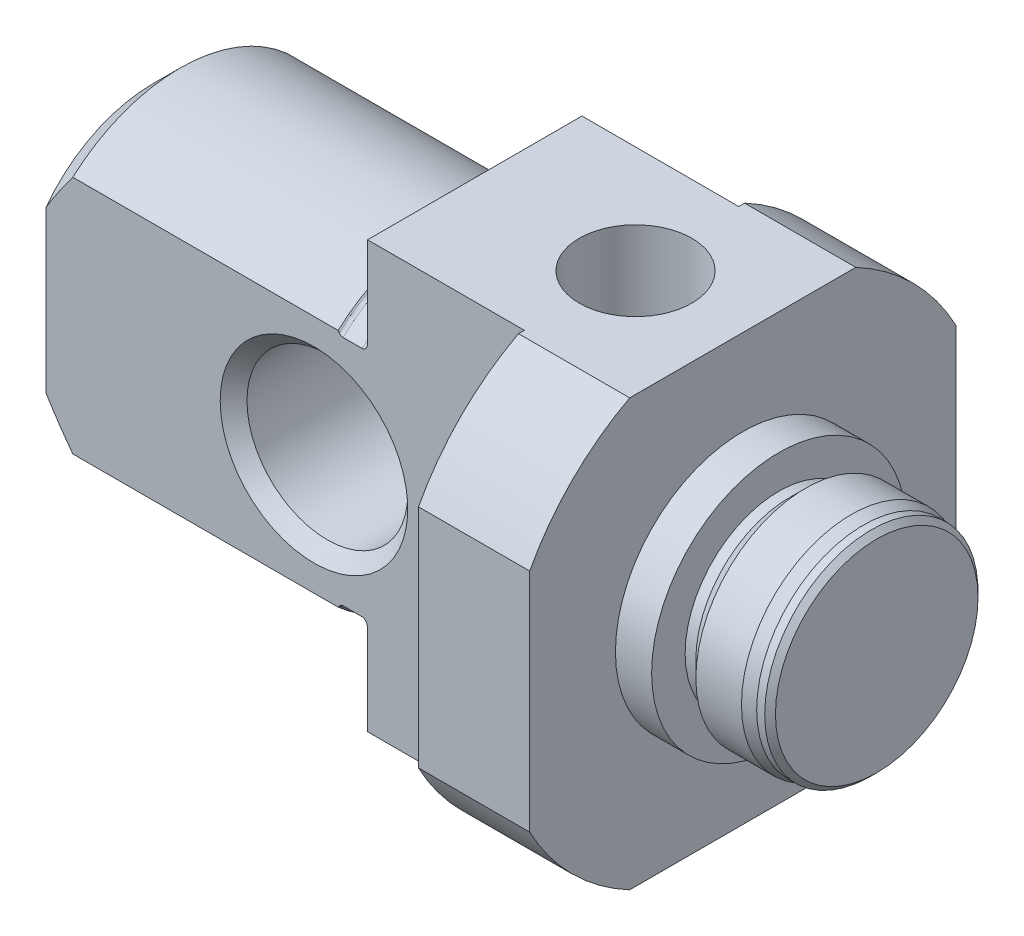
SolidWorks part; units mm, degrees
ref_plane "Front Plane" through (0, 0, 0) normal (0, 0, 1) x (1, 0, 0)
ref_plane "Top Plane" through (0, 0, 0) normal (0, 1, 0) x (1, 0, 0)
ref_plane "Right Plane" through (0, 0, 0) normal (1, 0, 0) x (0, 0, -1)
sketch "Sketch1" plane through (0, 0, 0) normal (0, 0, 1) x (1, 0, 0)
  line L0 (0, 0) -> (10860.2911, 0) construction
  line L1 (0, 0) -> (0, 10860.2911) construction
  line L2 (-22, 0) -> (-22, 5)
  line L3 (-21, 6) -> (-11.1, 6)
  line L4 (-11.1, 6) -> (-11.0586, 5.9586)
  line L5 (-10.9172, 5.9) -> (-10.2, 5.9)
  line L6 (-10, 6.1) -> (-10, 9)
  line L7 (-10, 9) -> (0, 9)
  line L8 (0, 9) -> (0, 4.75)
  line L9 (0, 4.75) -> (1.35, 4.75)
  line L10 (1.35, 4.75) -> (1.35, 3.5)
  line L11 (1.35, 3.5) -> (1.75, 3.5)
  line L12 (1.75, 3.5) -> (2.35, 4.1)
  line L13 (2.35, 4.1) -> (4.0522, 4.1)
  line L14 (4.0522, 4.1) -> (4.5, 3.98)
  line L15 (4.5, 3.98) -> (4.8, 3.98)
  line L16 (5, 3.78) -> (5, 0)
  line L17 (5, 0) -> (-22, 0)
  line L18 (4.8, 3.98) -> (5, 3.78)
  line L19 (-22, 5) -> (-21, 6)
  arc A0 (-10.2, 5.9) -> (-10, 6.1) centre (-10.2, 6.1) ccw
  arc A1 (-11.0586, 5.9586) -> (-10.9172, 5.9) centre (-10.9172, 6.1) ccw
  point P6 (-22, 6)
  point P20 (5, 3.98)
  point P27 (-10, 5.9)
  point P30 (-11, 5.9)
  dimension "AB-R" = 0.2
  dimension "I-Ø1" = 7
  dimension "E-Ø2" = 7.96
  dimension "E-Ø1" = 8.2
  dimension "O-Ø2" = 9.5
  dimension "O-Ø1" = 18
  dimension "T-Ø1" = 12
  dimension "L" = 27
  dimension "T-L" = 12
  dimension "A" = 0.4
  dimension "B2" = 3.65
  dimension "B1" = 5
  dimension "AB" = 1
  dimension "D13" = 45
  dimension "B3" = 0.5
  dimension "D15" = 15
  dimension "T-Ø2" = 11.8
  dimension "D17" = 45
  dimension "C-L2" = 0.2
  dimension "D19" = 45
  dimension "C-L1" = 1
  dimension "D21" = 45
revolve "Revolve1" add sketch "Sketch1" angle 360 about L0
cosmetic thread "Cosmetic Thread1" parameters "D2"=6.619
sketch "Sketch2" plane through (-10, 0, 0) normal (-1, 0, 0) x (0, 0, 1)
  line L0 (0, 0) -> (0, -50000) construction
  line L1 (-4.025, 7) -> (4.025, 7)
  line L2 (-4.225, 6.8) -> (-4.225, 7.9467)
  line L4 (4.225, 6.8) -> (4.225, 7.9467)
  circle A0 centre (0, 0) radius 9 construction
  arc A1 (4.225, 7.9467) -> (-4.225, 7.9467) centre (0, 0) ccw
  arc A2 (4.025, 7) -> (4.225, 6.8) centre (4.025, 6.8) cw
  arc A3 (-4.025, 7) -> (-4.225, 6.8) centre (-4.025, 6.8) ccw
  dimension "M-R1" = 0.2
  dimension "M-L" = 16
  dimension "M1" = 8.45
extrude "Boss-Extrude1" [suppressed] add sketch "Sketch2" against normal up to surface (15.5 mm away)
sketch "Sketch3" plane through (-22, 0, 0) normal (-1, 0, 0) x (0, 0, 1)
  line L0 (-4, 8.0623) -> (-4, -8.0623)
  line L1 (4, 8.0623) -> (4, -8.0623)
  line L2 (0, 0) -> (0, 18.183) construction
  arc A0 (4, -8.0623) -> (4, 8.0623) centre (0, 0) ccw
  circle A3 centre (0, 0) radius 9 construction
  arc A4 (-4, 8.0623) -> (-4, -8.0623) centre (0, 0) ccw
  dimension "X" = 8
extrude "O-L" cut sketch "Sketch3" against normal offset from surface (17.85 mm away) 5.5 up to face at (1.35, 0, 4.75)
sketch "Sketch6" plane through (-10, 0, 0) normal (-1, 0, 0) x (0, 0, 1)
  line L0 (0, 0) -> (0, 50000) construction
  line L1 (0, 0) -> (50000, 0) construction
  line L2 (-4.2187, 7.95) -> (4.2187, 7.95)
  line L3 (7.95, 4.2187) -> (7.95, -4.2187)
  line L4 (4.2187, -7.95) -> (-4.2187, -7.95)
  line L5 (-7.95, -4.2187) -> (-7.95, 4.2187)
  circle A0 centre (0, 0) radius 9 construction
  arc A1 (-7.95, 4.2187) -> (-7.95, -4.2187) centre (0, 0) ccw
  arc A2 (4.2187, 7.95) -> (-4.2187, 7.95) centre (0, 0) ccw
  arc A3 (7.95, -4.2187) -> (7.95, 4.2187) centre (0, 0) ccw
  arc A4 (-4.2187, -7.95) -> (4.2187, -7.95) centre (0, 0) ccw
  point P20 (0, 0)
  dimension "D1" = 15.9
  dimension "D2" = 4
extrude "Cut-Extrude4" cut sketch "Sketch6" against normal up to next
sketch "Sketch4" plane through (0, 0, 4) normal (0, 0, 1) x (1, 0, 0)
  line L0 (1.35, -4.75) -> (1.35, 4.75) construction
  circle A0 centre (-12, 0) radius 3
  dimension "ØN" = 6
  dimension "N-L" = 13.35
extrude "Cut-Extrude2" cut sketch "Sketch4" against normal up to next
chamfer "Chamfer4" distance 0.5 angle 45 2 edges at (-9, 0, -4) (-9, 0, 4)
hole_wizard "M5 Tapped Hole1" positions "Sketch7" profile "Sketch8" tap size "M5" standard "ISO"
sketch "Sketch7" plane through (0, 7.95, 0) normal (0, 1, 0) x (1, 0, 0)
  line L0 (0, 0) -> (-5.5462, 0) construction
  line L2 (0, -4.2187) -> (0, 4.2187) construction
  point P0 (-4, 0)
  dimension "D1" = 4
sketch "Sketch8" plane through (-4, 7.95, 0) normal (1, 0, 0) x (0, 0, 1)
  line L0 (0, 0) -> (0, 7.2124)
  line L1 (0, 7.2124) -> (2.1, 6)
  line L2 (2.1, 6) -> (2.1, 0)
  line L5 (2.1, 0) -> (0, 0)
  line L10 (0, 7.2124) -> (-2.1, 6) construction
  line L11 (0, -6.35) -> (0, 107.95) construction
  dimension "Tap Drill Dia." = 4.2
  dimension "Tap Drill Depth" = 6
  dimension "Drill Angle" = 120
cosmetic thread "Hole Thread1" parameters "D1"=5, "D2"=5
hole_wizard "M5 Tapped Hole2" [suppressed] positions "Sketch9" profile "Sketch10" tap size "M5" standard "IS"
sketch "Sketch9" plane through (0, 10.5, 0) normal (0, 1, 0) x (1, 0, 0)
  line L0 (0, 0) -> (-9.5002, 0) construction
  line L2 (0, 4.55) -> (0, -4.55) construction
  point P0 (-5.35, 0)
  dimension "D1" = 5.35
sketch "Sketch10" plane through (-5.35, 10.5, 0) normal (1, 0, 0) x (0, 0, 1)
  line L0 (0, 0) -> (0, 8.2124)
  line L1 (0, 8.2124) -> (2.1, 7)
  line L2 (2.1, 7) -> (2.1, 0)
  line L5 (2.1, 0) -> (0, 0)
  line L10 (0, 8.2124) -> (-2.1, 7) construction
  line L11 (0, -6.35) -> (0, 107.95) construction
  dimension "Tap Drill Dia." = 4.2
  dimension "Tap Drill Depth" = 7
  dimension "Drill Angle" = 120
cosmetic thread "Hole Thread2" [suppressed] parameters "D1"=6.5, "D2"=5
hole_wizard "G1/8 Tapped Hole1" [suppressed] positions "Sketch11" profile "Sketch12" tap size "G1/8" standard "IS"
sketch "Sketch11" plane through (0, 15.5, 0) normal (0, 1, 0) x (1, 0, 0)
  line L0 (0, 0) -> (-7.5, 0) construction
  line L2 (0, 6.8) -> (0, -6.8) construction
  point P0 (-7.5, 0)
  dimension "D1" = 7.5
sketch "Sketch12" plane through (-7.5, 15.5, 0) normal (1, 0, 0) x (0, 0, 1)
  line L0 (0, 0) -> (0, 11.6438)
  line L1 (0, 11.6438) -> (4.4, 9)
  line L2 (4.4, 9) -> (4.4, 0)
  line L5 (4.4, 0) -> (0, 0)
  line L10 (0, 11.6438) -> (-4.4, 9) construction
  line L11 (0, -6.35) -> (0, 107.95) construction
  dimension "Tap Drill Dia." = 8.8
  dimension "Tap Drill Depth" = 9
  dimension "Drill Angle" = 118
cosmetic thread "Hole Thread3" [suppressed] parameters "D1"=8.5, "D2"=9.728
